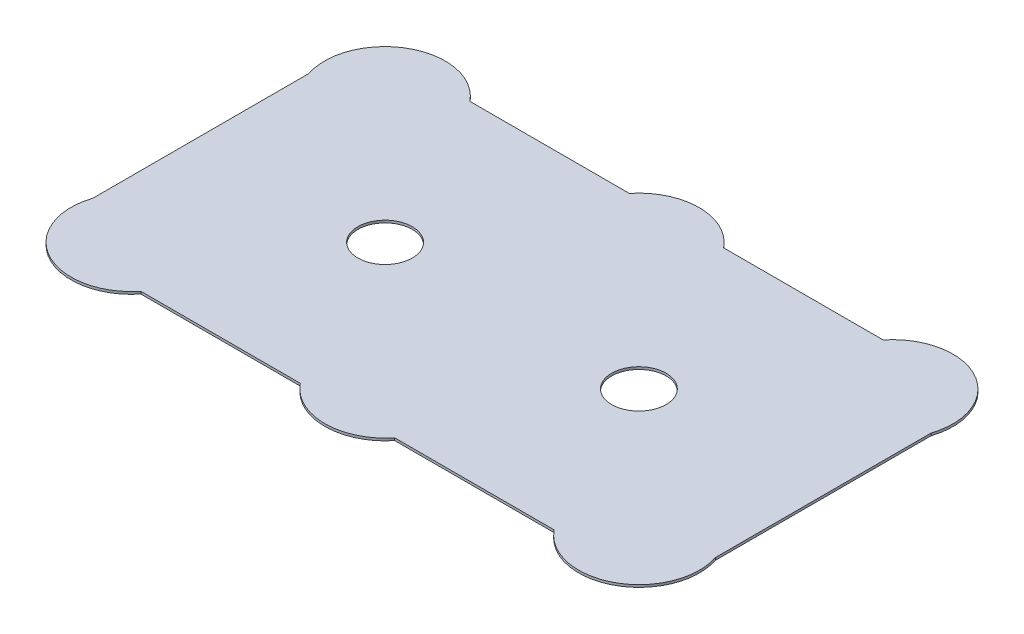
SolidWorks part; units mm, degrees
ref_plane "Front" through (0, 0, 0) normal (0, 0, 1) x (1, 0, 0)
ref_plane "Top" through (0, 0, 0) normal (0, 1, 0) x (1, 0, 0)
ref_plane "Right" through (0, 0, 0) normal (1, 0, 0) x (0, 0, -1)
sketch "Sketch1" plane through (0, 0, 0) normal (0, 1, 0) x (1, 0, 0)
  line L0 (0.25, 24.4088) -> (0.25, 6.5612)
  line L1 (0, 0) -> (52, 0) construction
  line L2 (0, 0) -> (0, 30.97) construction
  line L3 (0, 30.97) -> (52, 30.97) construction
  line L4 (52, 0) -> (52, 30.97) construction
  line L5 (51.75, 24.4088) -> (51.75, 6.5612)
  line L6 (8.9031, 29.095) -> (22.0969, 29.095)
  line L7 (29.9031, 29.095) -> (43.0969, 29.095)
  line L8 (8.9031, 1.875) -> (22.0969, 1.875)
  line L9 (29.9031, 1.875) -> (43.0969, 1.875)
  line L10 (51.75, 15.485) -> (0.25, 15.485) construction
  line L11 (36.5, 15.485) -> (15.5, 15.485)
  arc A0 (8.9031, 29.095) -> (0.25, 24.4088) centre (5, 25.97) ccw
  arc A1 (0.25, 6.5612) -> (8.9031, 1.875) centre (5, 5) ccw
  arc A2 (43.0969, 1.875) -> (51.75, 6.5612) centre (47, 5) ccw
  arc A3 (51.75, 24.4088) -> (43.0969, 29.095) centre (47, 25.97) ccw
  arc A4 (22.0969, 1.875) -> (29.9031, 1.875) centre (26, 5) ccw
  arc A5 (29.9031, 29.095) -> (22.0969, 29.095) centre (26, 25.97) ccw
  circle A6 centre (15.5, 15.485) radius 2.25
  circle A7 centre (36.5, 15.485) radius 2.25
  point P20 (26, 0)
  point P36 (36.5, 15.485)
  point P38 (26, 15.485)
  dimension "D3" = 10
  dimension "D9" = 4.5
  dimension "D1" = 52
  dimension "D2" = 30.97
  dimension "D4" = 0.5
  dimension "D5" = 0.5
  dimension "D6" = 3.75
  dimension "D7" = 3.75
  dimension "D8" = 21
extrude "Boss-Extrude1" add sketch "Sketch1" along normal blind 0.2
